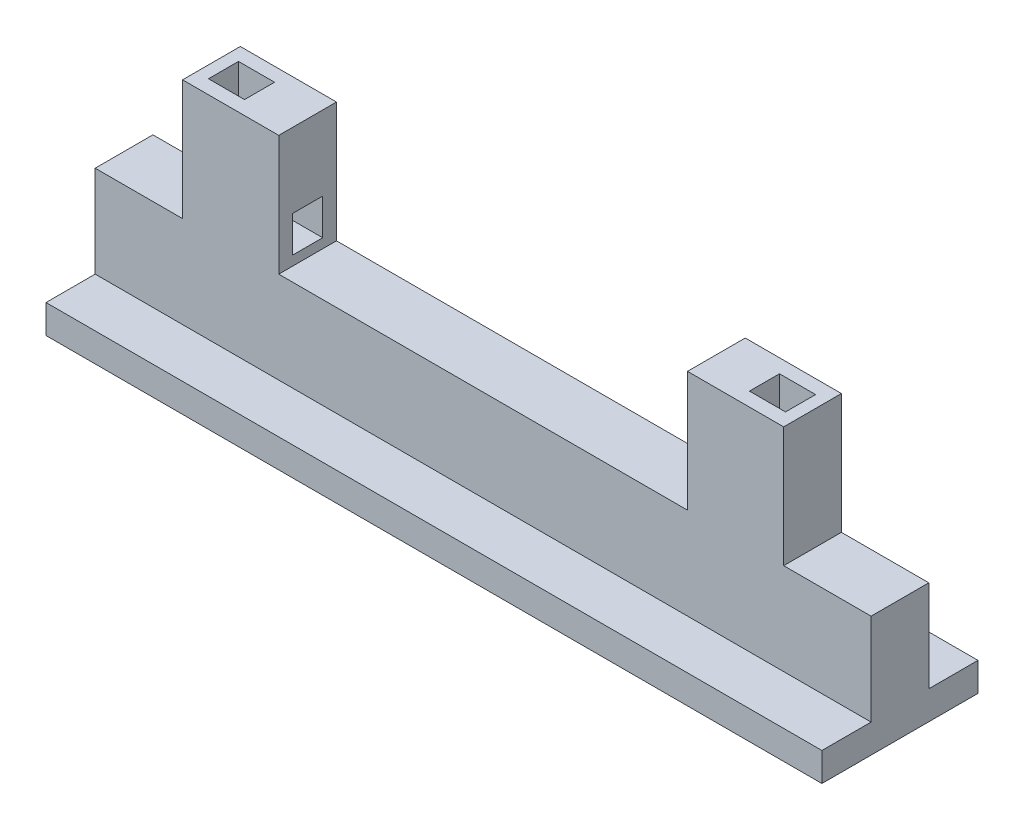
SolidWorks part; units mm, degrees
ref_plane "Front Plane" through (0, 0, 0) normal (0, 0, 1) x (1, 0, 0)
ref_plane "Top Plane" through (0, 0, 0) normal (0, 1, 0) x (1, 0, 0)
ref_plane "Right Plane" through (0, 0, 0) normal (1, 0, 0) x (0, 0, -1)
sketch "Sketch3" plane through (0, 0, 0) normal (1, 0, 0) x (0, 0, -1)
  line L0 (0.543, -11.9498) -> (0.543, -6) construction
  line L1 (-5.9491, -11.9498) -> (7.0352, -11.9498)
  line L2 (-5.9491, -11.9498) -> (-5.9491, -14.3306)
  line L3 (-5.9491, -14.3306) -> (7.0352, -14.3306)
  line L4 (7.0352, -11.9498) -> (7.0352, -14.3306)
  line L6 (-1.8585, -4.318) -> (2.9446, -4.318)
  line L7 (-1.8585, -4.318) -> (-1.8585, -13.6318)
  line L8 (-1.8585, -13.6318) -> (2.9446, -13.6318)
  line L9 (2.9446, -4.318) -> (2.9446, -13.6318)
  line L10 (-1.8585, -4.318) -> (2.9446, -13.6318) construction
  line L11 (-1.8585, -13.6318) -> (2.9446, -4.318) construction
  point P9 (0.543, -8.9749)
extrude "Boss-Extrude2" add sketch "Sketch3" along normal blind 32.27 contours L9 L8 L7 L6 | L3 L4 L1 L2
ref_plane "Plane1" through (0, 0, -0.543) normal (0, 0, -1) x (-1, 0, 0)
sketch "Sketch6" plane through (0, -4.318, 0) normal (0, 1, 0) x (1, 0, 0)
  line L1 (32.27, 2.9446) -> (0, 2.9446) construction
  line L2 (7.27, 2.9446) -> (15.27, 2.9446)
  line L3 (16.135, 0.543) -> (16.135, 2.9446) construction
  line L4 (32.27, 2.9446) -> (0, 2.9446) construction
  line L5 (16.135, 0.543) -> (16.135, -1.8585) construction
  line L6 (0, -1.8585) -> (32.27, -1.8585) construction
  line L9 (7.27, 2.9446) -> (7.27, -1.8585)
  line L10 (7.27, -1.8585) -> (15.27, -1.8585)
  line L11 (15.27, 2.9446) -> (15.27, -1.8585)
  line L12 (32.27, -1.8585) -> (0, -1.8585) construction
  line L13 (32.27, -1.8585) -> (32.27, 2.9446) construction
  dimension "D1" = 17
  dimension "D2" = 8
extrude "Boss-Extrude3" add sketch "Sketch6" along normal blind 10
sketch "Sketch7" plane through (0, 0, -0.543) normal (0, 0, 1) x (1, 0, 0)
  line L0 (7.27, 5.682) -> (15.27, 5.682) construction
  line L1 (11.27, 5.682) -> (8.27, 5.682)
  line L2 (11.27, 5.682) -> (11.27, -0.5204)
  line L3 (11.27, -0.5204) -> (8.27, -0.5204)
  line L4 (8.27, 5.682) -> (8.27, -0.5204)
  line L5 (15.27, 5.682) -> (15.27, -4.318) construction
  line L7 (11.27, -0.5204) -> (15.27, -0.5204)
  line L8 (11.27, -0.5204) -> (11.27, -3.5204)
  line L9 (11.27, -3.5204) -> (15.27, -3.5204)
  line L10 (15.27, -0.5204) -> (15.27, -3.5204)
  circle A0 centre (11.27, -0.5204) radius 3
  point P12 (0, 0)
  dimension "D1" = 4
  dimension "D2" = 3
extrude "Cut-Extrude2" cut sketch "Sketch7" against normal mid plane 2.5 contours L2 A0 L4 L1 | A0 L2 L3 | A0 L3 L8 | A0 L8 L7
fillet "Fillet1" radius 3 1 edges at (11.27, -0.5204, -0.543)
mirror "Mirror2" about plane through (32.27, 0, 0) normal (-1, 0, 0) of "Cut-Extrude2", "Boss-Extrude3", "Boss-Extrude2"
